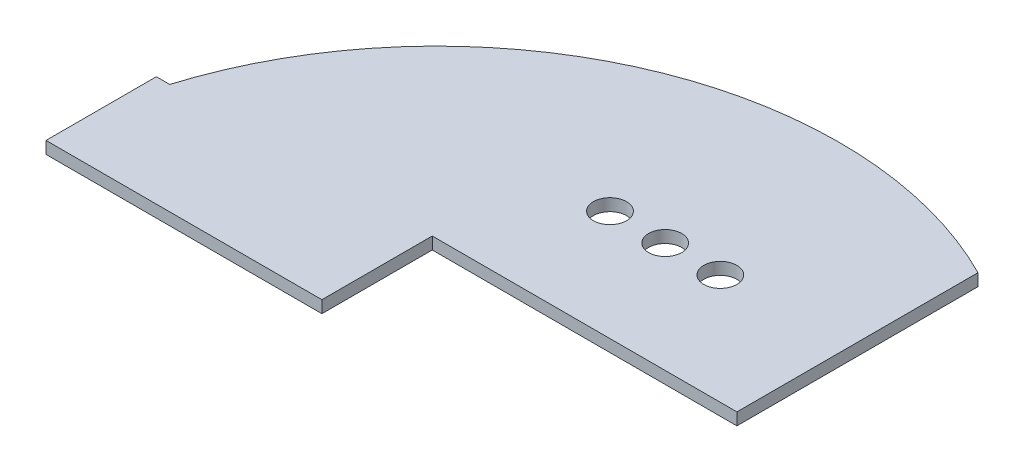
SolidWorks part; units mm, degrees
ref_plane "Front Plane" through (0, 0, 0) normal (0, 0, 1) x (1, 0, 0)
ref_plane "Top Plane" through (0, 0, 0) normal (0, 1, 0) x (1, 0, 0)
ref_plane "Right Plane" through (0, 0, 0) normal (1, 0, 0) x (0, 0, -1)
sketch "Sketch1" plane through (0, 0, 0) normal (0, 1, 0) x (1, 0, 0)
  line L1 (-72.2104, 1.42) -> (-22.2104, 1.42)
  line L2 (-22.2104, 1.42) -> (-22.2104, 21.42)
  line L3 (-22.2104, 21.42) -> (37.9996, 21.42) construction
  line L4 (37.9996, 21.42) -> (37.9996, 62.33) construction
  line L5 (75.5176, 0) -> (-98.8929, 0) construction
  line L6 (-72.2104, 1.42) -> (-72.2104, 21.42)
  line L7 (-72.2104, 21.42) -> (-69.7867, 21.42)
  line L8 (32.9996, 65.1155) -> (32.9996, 21.42)
  line L9 (32.9996, 21.42) -> (-22.2104, 21.42)
  arc A1 (-69.7867, 21.42) -> (37.9996, 62.33) centre (0, 0) cw construction
  arc A2 (-69.7867, 21.42) -> (32.9996, 65.1155) centre (0, 0) cw
  dimension "D1" = 73
  dimension "D2" = 50
  dimension "D3" = 20
  dimension "D4" = 21.42
  dimension "D5" = 124.66
  dimension "D6" = 60.21
  dimension "D7" = 5
extrude "Boss-Extrude1" add sketch "Sketch1" along normal mid plane 2.2
sketch "Sketch2" plane through (0, 1.1, 0) normal (0, 1, 0) x (1, 0, 0)
  line L0 (-10, 41.42) -> (10, 41.42) construction
  line L1 (-22.2104, 21.42) -> (32.9996, 21.42) construction
  circle A0 centre (0, 41.42) radius 3
  circle A1 centre (10, 41.42) radius 3
  circle A2 centre (-10, 41.42) radius 3
  point P6 (0, 0)
  point P7 (0, 0)
  dimension "D1" = 6
  dimension "D2" = 20
  dimension "D3" = 20
extrude "Cut-Extrude1" cut sketch "Sketch2" against normal through all
